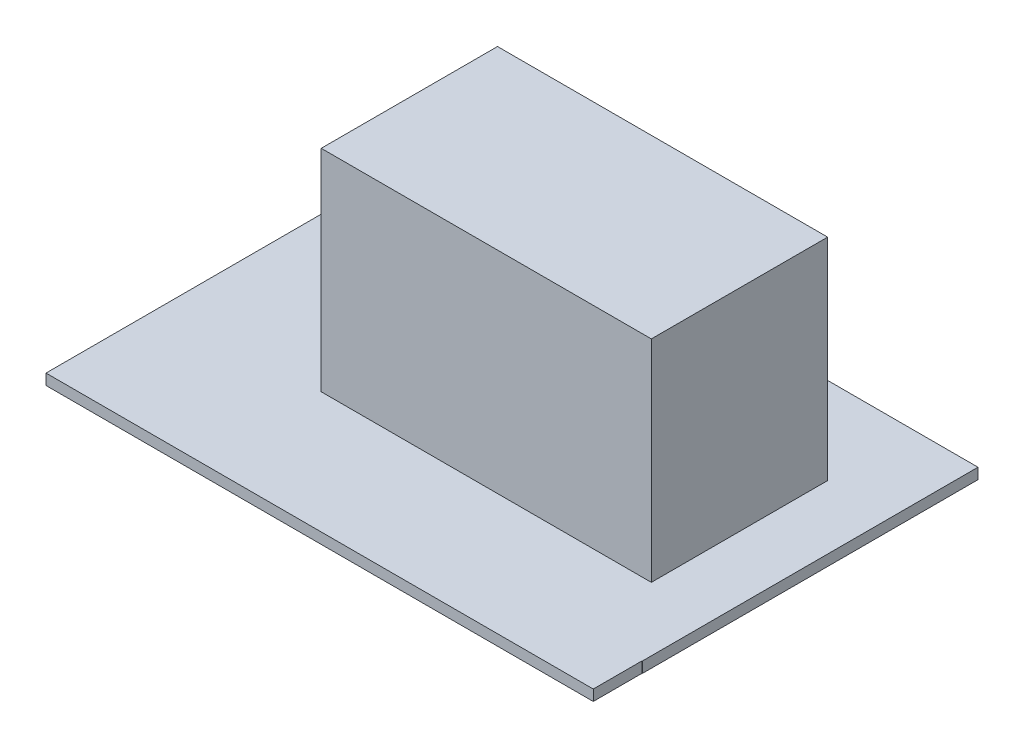
SolidWorks part; units mm, degrees
ref_plane "Front Plane" through (0, 0, 0) normal (0, 0, 1) x (1, 0, 0)
ref_plane "Top Plane" through (0, 0, 0) normal (0, 1, 0) x (1, 0, 0)
ref_plane "Right Plane" through (0, 0, 0) normal (1, 0, 0) x (0, 0, -1)
sketch "Sketch1" plane through (0, 0, 0) normal (0, 1, 0) x (1, 0, 0)
  line L0 (0, 0) -> (0, -25.4)
  line L1 (0, -25.4) -> (13.2588, -56.388)
  line L2 (13.2588, -56.388) -> (31.9532, -56.388)
  line L3 (31.9532, -56.388) -> (31.9532, -49.3268)
  line L4 (31.9532, -49.3268) -> (80.4672, -49.3268)
  line L5 (80.4672, -49.3268) -> (80.4672, 0)
  line L6 (80.4672, 0) -> (0, 0)
  dimension "D1" = 80.4672
  dimension "D2" = 49.3268
  dimension "D3" = 56.388
  dimension "D4" = 25.4
  dimension "D5" = 48.514
  dimension "D6" = 18.6944
extrude "Boss-Extrude1" add sketch "Sketch1" along normal blind 1.5875
sketch "Sketch2" plane through (0, 0, 0) normal (0, -1, 0) x (1, 0, 0)
  line L1 (36.068, 0) -> (0, 0)
  line L2 (36.068, 0) -> (36.068, 1.5875)
  line L3 (36.068, 1.5875) -> (0, 1.5875)
  line L4 (0, 0) -> (0, 1.5875)
  dimension "D1" = 1.5875
  dimension "D2" = 36.068
extrude "Boss-Extrude2" add sketch "Sketch2" along normal blind 21.2725
sketch "Sketch3" plane through (0, 0, 1.5875) normal (0, 0, 1) x (1, 0, 0)
  line L0 (36.068, -21.2725) -> (36.068, 0) construction
  line L1 (36.068, -9.144) -> (34.4805, -9.144)
  line L2 (36.068, -9.144) -> (36.068, -34.798)
  line L3 (36.068, -34.798) -> (34.4805, -34.798)
  line L4 (34.4805, -9.144) -> (34.4805, -34.798)
  line L5 (36.068, 0) -> (0, 0) construction
  line L7 (18.034, 0) -> (18.034, -21.2725) construction
  line L9 (36.068, -21.2725) -> (0, -21.2725) construction
  line L10 (1.5875, -9.144) -> (1.5875, -34.798)
  line L11 (0, -34.798) -> (1.5875, -34.798)
  line L12 (0, -9.144) -> (0, -34.798)
  line L13 (0, -9.144) -> (1.5875, -9.144)
  dimension "D1" = 1.5875
  dimension "D2" = 9.144
  dimension "D3" = 34.798
extrude "Boss-Extrude3" add sketch "Sketch3" along normal blind 6.35
hole_wizard "Hole1" positions "Sketch6" profile "Sketch5" legacy
sketch "Sketch6" plane through (0, 0, 0) normal (0, 0, -1) x (-1, 0, 0)
  line L0 (-18.034, -21.2725) -> (-18.034, 1.5875) construction
  line L1 (0, -21.2725) -> (-36.068, -21.2725) construction
  line L2 (-80.4672, 1.5875) -> (0, 1.5875) construction
  line L12 (0, -9.8425) -> (-80.4672, -9.8425) construction
  line L13 (0, -21.2725) -> (0, 1.5875) construction
  line L14 (-80.4672, 1.5875) -> (-80.4672, 0) construction
  point P0 (-18.034, -9.8425)
sketch "Sketch5" plane through (18.034, -9.8425, 0) normal (1, 0, 0) x (0, 1, 0)
  line L0 (0, 0) -> (0, 15.875)
  line L1 (0, 15.875) -> (2.54, 15.875)
  line L2 (2.54, 15.875) -> (2.54, 0)
  line L3 (2.54, 0) -> (0, 0)
  line L4 (0, 110) -> (0, -10) construction
  dimension "Diameter" = 5.08
  dimension "Depth" = 15.875
sketch "Sketch9" plane through (0, 1.5875, 0) normal (0, 1, 0) x (1, 0, 0)
  line L0 (0, 0) -> (0, -25.4) construction
  line L1 (71.12, -12.7508) -> (22.606, -12.7508)
  line L2 (71.12, -12.7508) -> (71.12, -38.6588)
  line L3 (71.12, -38.6588) -> (22.606, -38.6588)
  line L4 (22.606, -12.7508) -> (22.606, -38.6588)
  line L5 (31.9532, -49.3268) -> (80.4672, -49.3268) construction
  dimension "D1" = 48.514
  dimension "D2" = 25.908
  dimension "D3" = 22.606
  dimension "D4" = 10.668
extrude "Boss-Extrude4" add sketch "Sketch9" along normal blind 30.988
ref_point "Point5"
sketch "Sketch11" plane through (0, 1.5875, 0) normal (0, 1, 0) x (1, 0, 0)
  line L1 (0, 0) -> (80.4243, 0)
  line L2 (0, 0) -> (0, -56.4985)
  line L3 (0, -56.4985) -> (80.4243, -56.4985)
  line L4 (80.4243, 0) -> (80.4243, -56.4985)
extrude "Boss-Extrude5" add sketch "Sketch11" against normal up to surface (1.5875 mm away) up to face at (38.941, 0, 25.2561)
